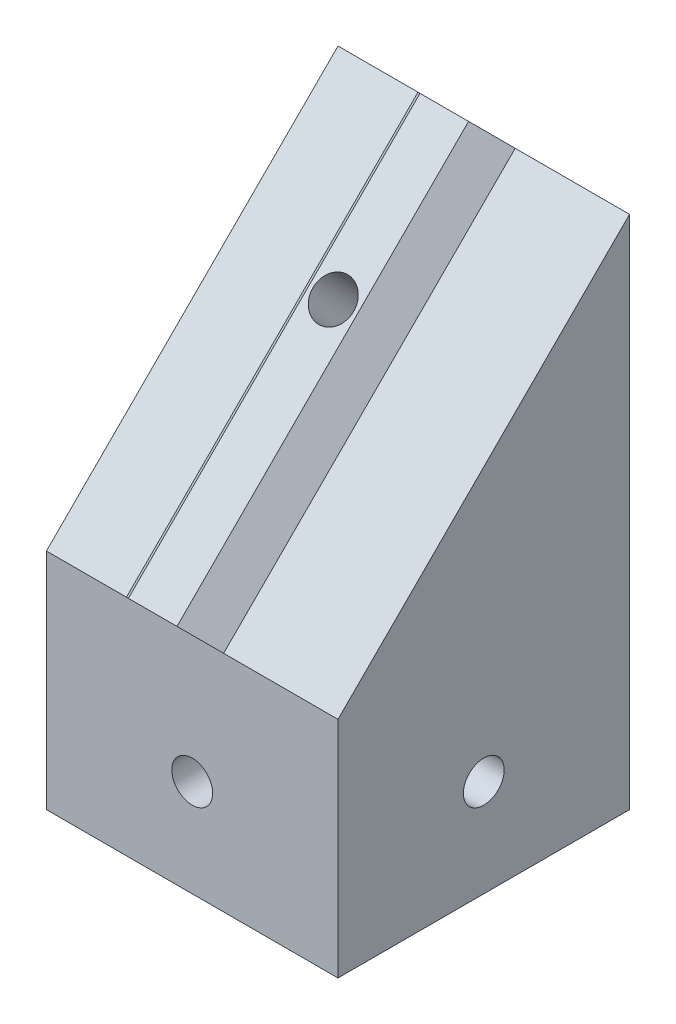
SolidWorks part; units mm, degrees
ref_plane "Front Plane" through (0, 0, 0) normal (0, 0, 1) x (1, 0, 0)
ref_plane "Top Plane" through (0, 0, 0) normal (0, 1, 0) x (1, 0, 0)
ref_plane "Right Plane" through (0, 0, 0) normal (1, 0, 0) x (0, 0, -1)
sketch "Sketch1" plane through (0, 0, 0) normal (0, 1, 0) x (1, 0, 0)
  line L0 (-15, -15) -> (-15, 15)
  line L1 (10, -10) -> (-10, -10)
  line L2 (10, -10) -> (10, 10)
  line L3 (10, 10) -> (-10, 10)
  line L4 (-10, -10) -> (-10, 10)
  line L5 (10, -10) -> (-10, 10) construction
  line L6 (10, 10) -> (-10, -10) construction
  line L7 (15, 15) -> (-15, 15)
  line L8 (15, -15) -> (15, 15)
  line L9 (15, -15) -> (-15, -15)
  point P0 (0, 0)
  dimension "D1" = 20
  dimension "D2" = 20
  dimension "D3" = 5
extrude "Boss-Extrude1" add sketch "Sketch1" along normal blind 20
sketch "Sketch2" plane through (0, 20, 0) normal (0, 1, 0) x (1, 0, 0)
  line L0 (4, -2.3365) -> (4, 2.6635)
  line L1 (8, -2.3555) -> (8, 2.3555)
  line L2 (8, -5.0498) -> (8, 4.9502)
  line L3 (10, -10) -> (10, 10) construction
  line L4 (4, 2.6635) -> (8, 4.9502)
  line L5 (4, -2.3365) -> (8, -5.0498)
  line L6 (8, -2.3555) -> (10, -2.3555)
  line L7 (8, 2.3555) -> (10, 2.3555)
  line L8 (10, 2.3555) -> (10, -2.3555)
  line L9 (-2.3365, -4) -> (-5.0498, -8)
  line L10 (-5.0498, -8) -> (4.9502, -8)
  line L11 (2.6635, -4) -> (4.9502, -8)
  line L12 (-2.3365, -4) -> (2.6635, -4)
  line L13 (2.3555, -10) -> (-2.3555, -10)
  line L14 (-2.3555, -8) -> (-2.3555, -10)
  line L15 (-2.3555, -8) -> (2.3555, -8)
  line L16 (2.3555, -8) -> (2.3555, -10)
  line L17 (-4, 2.3365) -> (-8, 5.0498)
  line L18 (-8, 5.0498) -> (-8, -4.9502)
  line L19 (-4, -2.6635) -> (-8, -4.9502)
  line L20 (-4, 2.3365) -> (-4, -2.6635)
  line L21 (-10, -2.3555) -> (-10, 2.3555)
  line L22 (-8, 2.3555) -> (-10, 2.3555)
  line L23 (-8, 2.3555) -> (-8, -2.3555)
  line L24 (-8, -2.3555) -> (-10, -2.3555)
  line L25 (2.3365, 4) -> (5.0498, 8)
  line L26 (5.0498, 8) -> (-4.9502, 8)
  line L27 (-2.6635, 4) -> (-4.9502, 8)
  line L28 (2.3365, 4) -> (-2.6635, 4)
  line L29 (-2.3555, 10) -> (2.3555, 10)
  line L30 (2.3555, 8) -> (2.3555, 10)
  line L31 (2.3555, 8) -> (-2.3555, 8)
  line L32 (-2.3555, 8) -> (-2.3555, 10)
  point P3 (4, 0.1635)
  point P6 (8, 0)
  point P9 (8, -0.0498)
  point P40 (0, 0)
  line M9 (-10, 10) -> (10, 10)
  line M10 (10, 10) -> (10, -10)
  line M11 (10, -10) -> (-10, -10)
  dimension "D1" = 2
  dimension "D2" = 10
  dimension "D3" = 5
  dimension "D4" = 0
  dimension "D5" = 4
  dimension "D7" = 4.711
  dimension "D6" = 4
extrude "Boss-Extrude2" add sketch "Sketch2" against normal blind 20 separate body contours L28 L25 L26 L27 | L32 L26 L30 M9 | L20 L17 L18 L19 | L12 L9 L10 L11 | L16 L10 L14 M11 | L0 L5 L2 L1 L4 | L7 L1 L6 M10 | L21 L22 L23 L24
sketch "Sketch3" plane through (-15, 0, 0) normal (-1, 0, 0) x (0, 0, 1)
  circle A0 centre (0, 10) radius 2.1
  dimension "D1" = 4.2
extrude "Cut-Extrude1" cut sketch "Sketch3" against normal through all
sketch "Sketch4" plane through (0, 0, -15) normal (0, 0, -1) x (-1, 0, 0)
  circle A0 centre (0, 10) radius 2.1
  dimension "D1" = 4.2
extrude "Cut-Extrude2" cut sketch "Sketch4" against normal through all
sketch "Sketch5" plane through (15, 0, 0) normal (1, 0, 0) x (0, 0, -1)
  line L0 (-15, 20) -> (15, 50)
  line L1 (-15, 20) -> (15, 20) construction
  line L2 (-15, 20) -> (-15, 23.0499)
  line L3 (-15, 23.0499) -> (15, 53.0499)
  line L4 (15, 53.0499) -> (15, 50)
  line L5 (15, 20) -> (15, 0) construction
  line L6 (15, 53.0499) -> (15, 20)
  line L7 (15, 50) -> (15, 20)
  line L8 (-15, 20) -> (15, 20)
  line M8 (15, 20) -> (-15, 20)
  dimension "D1" = 45
  dimension "D2" = 0
extrude "Boss-Extrude3" add sketch "Sketch5" against normal blind 30 contours L4 L3 L2 L0 | L6 L0 M8
ref_plane "Plane1" through (0, 34.0249, -34.0249) normal (0, -0.7071, 0.7071) x (1, 0, 0)
sketch "Sketch8" plane through (0, 34.0249, -34.0249) normal (0, -0.7071, 0.7071) x (1, 0, 0)
  line L0 (-2.5, 32.6553) -> (2.5, 32.6553)
  line L1 (-2.3555, 29.4053) -> (2.3555, 29.4053)
  line L2 (-5, 29.4053) -> (5, 29.4053)
  line L3 (2.5, 32.6553) -> (5, 29.4053)
  line L4 (-2.5, 32.6553) -> (-5, 29.4053)
  line L5 (-2.3555, 29.4053) -> (-2.3555, 26.9053)
  line L6 (2.3555, 29.4053) -> (2.3555, 26.9053)
  line L7 (2.3555, 26.9053) -> (-2.3555, 26.9053)
  line L8 (-15, 26.9053) -> (15, 26.9053) construction
  line L11 (-15, 26.9053) -> (15, 26.9053) construction
  point P2 (0, 32.6553)
  point P5 (0, 29.4053)
  point P8 (0, 29.4053)
  point P11 (0, 26.9053)
  point P14 (0, 26.9053)
  dimension "D1" = 2.6445
  dimension "D2" = 4.711
  dimension "D3" = 10
  dimension "D4" = 5
  dimension "D5" = 3.25
  dimension "D6" = 2.5
  dimension "D7" = 2.5
extrude "Boss-Extrude4" add sketch "Sketch8" along normal blind 42.4264 contours L0 L4 L2 L1 L3 | L7 L6 L1 L5
sketch "Sketch9" plane through (0, 23.0908, 23.0908) normal (0, 0.7071, 0.7071) x (1, 0, 0)
  circle A1 centre (0, 31.9681) radius 2.1
  dimension "D1" = 4.2
extrude "Cut-Extrude3" cut sketch "Sketch9" against normal through all
